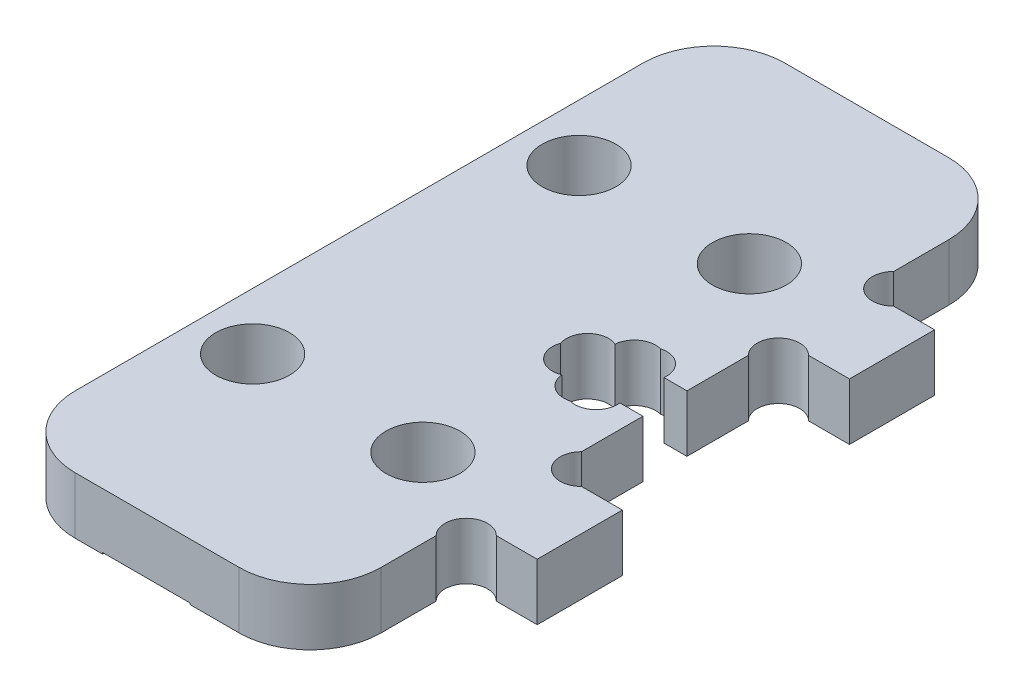
SolidWorks part; units mm, degrees
ref_plane "Alzado" through (0, 0, 0) normal (0, 0, 1) x (1, 0, 0)
ref_plane "Planta" through (0, 0, 0) normal (0, 1, 0) x (1, 0, 0)
ref_plane "Vista lateral" through (0, 0, 0) normal (1, 0, 0) x (0, 0, -1)
sketch "Croquis1" plane through (0, 0, 0) normal (0, 1, 0) x (1, 0, 0)
  line L0 (13.275, 14) -> (13.275, -14) construction
  line L1 (-5.775, -25) -> (5.775, -25)
  line L2 (-10.775, -20) -> (-10.775, 20)
  line L3 (-5.775, 25) -> (5.775, 25)
  line L4 (10.775, -20) -> (10.775, -14)
  line L5 (-10.775, -25) -> (10.775, 25) construction
  line L6 (-10.775, 25) -> (10.775, -25) construction
  line L7 (10.775, 14) -> (15.775, 14)
  line L8 (10.775, -8) -> (10.775, -1.55)
  line L9 (10.775, 8) -> (15.775, 8)
  line L10 (15.775, 14) -> (15.775, 8)
  line L11 (10.775, -8) -> (15.775, -8)
  line L12 (15.775, 11) -> (8.3263, 11) construction
  line L13 (10.775, -14) -> (15.775, -14)
  line L14 (15.775, -8) -> (15.775, -14)
  line L15 (0, 0) -> (13.275, 0) construction
  line L16 (10.775, 14) -> (10.775, 20)
  line L17 (8.725, -1.55) -> (8.725, -2.8)
  line L18 (5.825, 2.8) -> (8.725, 2.8)
  line L19 (5.825, 2.8) -> (5.825, 1.55)
  line L20 (5.825, -2.8) -> (8.725, -2.8)
  line L21 (8.725, 2.8) -> (8.725, 1.55)
  line L22 (3.775, 1.55) -> (5.825, 1.55)
  line L23 (3.775, 1.55) -> (3.775, -1.55)
  line L24 (3.775, -1.55) -> (5.825, -1.55)
  line L25 (10.775, 1.55) -> (10.775, 8)
  line L26 (8.725, 1.55) -> (10.775, 1.55)
  line L27 (5.825, -1.55) -> (5.825, -2.8)
  line L28 (8.725, -1.55) -> (10.775, -1.55)
  line L29 (3.775, 0) -> (0, 0) construction
  line L30 (7.275, 2.8) -> (7.275, -2.8) construction
  line L31 (7.275, 0) -> (3.775, 0) construction
  arc A0 (-5.775, -25) -> (-10.775, -20) centre (-5.775, -20) cw
  arc A1 (5.775, -25) -> (10.775, -20) centre (5.775, -20) ccw
  arc A2 (5.775, 25) -> (10.775, 20) centre (5.775, 20) cw
  arc A3 (-10.775, 20) -> (-5.775, 25) centre (-5.775, 20) cw
  point P0 (0, 0)
  dimension "D3" = 5
  dimension "D4" = 6
  dimension "D1" = 50
  dimension "D2" = 21.55
  dimension "D5" = 5
  dimension "D6" = 14
  dimension "D7" = 3.1
  dimension "D8" = 5.6
  dimension "D9" = 2.9
  dimension "D10" = 7
  dimension "D11" = 3.5
extrude "Saliente-Extruir1" add sketch "Croquis1" along normal blind 4
sketch "Croquis4" plane through (0, 0, 0) normal (0, 1, 0) x (1, 0, 0)
  line L1 (-3.85, 26.5) -> (2.3, 26.5)
  line L2 (-3.85, 26.5) -> (-3.85, -26.5)
  line L3 (-3.85, -26.5) -> (2.3, -26.5)
  line L4 (2.3, 26.5) -> (2.3, -26.5)
  line L6 (-0.775, 26.5) -> (-0.775, -26.5) construction
  line L7 (10.775, -20) -> (10.775, -14) construction
  line L8 (5.775, 25) -> (-5.775, 25) construction
  line L9 (-5.775, -25) -> (5.775, -25) construction
  dimension "D1" = 6.15
  dimension "D2" = 11.55
  dimension "D3" = 1.5
  dimension "D4" = 1.5
sketch "Croquis5" plane through (0, 4, 0) normal (0, 1, 0) x (1, 0, 0)
  line L0 (10.775, 0) -> (-10.775, 0) construction
  line L2 (-10.775, 20) -> (-10.775, -20) construction
  line L3 (-6.775, 11.5) -> (5.225, 11.5) construction
  line L4 (-0.775, 11.5) -> (-0.775, 26.5) construction
  line L6 (10.775, 8) -> (10.775, -8) construction
  circle A0 centre (-6.775, 11.5) radius 2.6
  circle A1 centre (5.225, 11.5) radius 2.6
  circle A2 centre (5.225, -11.5) radius 2.6
  circle A3 centre (-6.775, -11.5) radius 2.6
  dimension "D1" = 5.2
  dimension "D2" = 12
  dimension "D3" = 15
extrude "Cortar-Extruir3" cut sketch "Croquis5" against normal through all
sketch "Croquis9" plane through (0, 4, 0) normal (0, 1, 0) x (1, 0, 0)
  line L24 (-5.775, -25) -> (5.775, -25)
  line L25 (10.775, -20) -> (10.775, -14)
  line L26 (10.775, -14) -> (15.775, -14)
  line L27 (15.775, -14) -> (15.775, -8)
  line L28 (15.775, -8) -> (10.775, -8)
  line L29 (10.775, -8) -> (10.775, -1.55)
  line L30 (10.775, -1.55) -> (8.725, -1.55)
  line L31 (8.725, -1.55) -> (8.725, -2.8)
  line L32 (8.725, -2.8) -> (5.825, -2.8)
  line L33 (5.825, -2.8) -> (5.825, -1.55)
  line L34 (5.825, -1.55) -> (3.775, -1.55)
  line L35 (3.775, -1.55) -> (3.775, 1.55)
  line L36 (3.775, 1.55) -> (5.825, 1.55)
  line L37 (5.825, 1.55) -> (5.825, 2.8)
  line L38 (5.825, 2.8) -> (8.725, 2.8)
  line L39 (8.725, 2.8) -> (8.725, 1.55)
  line L40 (8.725, 1.55) -> (10.775, 1.55)
  line L41 (10.775, 1.55) -> (10.775, 8)
  line L42 (10.775, 8) -> (15.775, 8)
  line L43 (15.775, 8) -> (15.775, 14)
  line L44 (15.775, 14) -> (10.775, 14)
  line L45 (10.775, 14) -> (10.775, 20)
  line L46 (5.775, 25) -> (-5.775, 25)
  line L47 (-10.775, 20) -> (-10.775, -20)
  line L48 (-5.775, -25) -> (5.775, -25)
  line L49 (10.775, -20) -> (10.775, -14)
  line L50 (10.775, -14) -> (15.775, -14)
  line L51 (15.775, -14) -> (15.775, -8)
  line L52 (15.775, -8) -> (10.775, -8)
  line L53 (10.775, -8) -> (10.775, -1.55)
  line L54 (10.775, -1.55) -> (8.725, -1.55)
  line L55 (8.725, -1.55) -> (8.725, -2.8)
  line L56 (8.725, -2.8) -> (5.825, -2.8)
  line L57 (5.825, -2.8) -> (5.825, -1.55)
  line L58 (5.825, -1.55) -> (3.775, -1.55)
  line L59 (3.775, -1.55) -> (3.775, 1.55)
  line L60 (3.775, 1.55) -> (5.825, 1.55)
  line L61 (5.825, 1.55) -> (5.825, 2.8)
  line L62 (5.825, 2.8) -> (8.725, 2.8)
  line L63 (8.725, 2.8) -> (8.725, 1.55)
  line L64 (8.725, 1.55) -> (10.775, 1.55)
  line L65 (10.775, 1.55) -> (10.775, 8)
  line L66 (10.775, 8) -> (15.775, 8)
  line L67 (15.775, 8) -> (15.775, 14)
  line L68 (15.775, 14) -> (10.775, 14)
  line L69 (10.775, 14) -> (10.775, 20)
  line L70 (5.775, 25) -> (-5.775, 25)
  line L71 (-10.775, 20) -> (-10.775, -20)
  arc A4 (-10.775, -20) -> (-5.775, -25) centre (-5.775, -20) ccw
  arc A5 (5.775, -25) -> (10.775, -20) centre (5.775, -20) ccw
  arc A6 (10.775, 20) -> (5.775, 25) centre (5.775, 20) ccw
  arc A7 (-5.775, 25) -> (-10.775, 20) centre (-5.775, 20) ccw
  arc A8 (-10.775, -20) -> (-5.775, -25) centre (-5.775, -20) ccw
  arc A9 (5.775, -25) -> (10.775, -20) centre (5.775, -20) ccw
  arc A10 (10.775, 20) -> (5.775, 25) centre (5.775, 20) ccw
  arc A11 (-5.775, 25) -> (-10.775, 20) centre (-5.775, 20) ccw
  dimension "D1" = 0
sketch "Croquis6" plane through (0, 4, 0) normal (0, 1, 0) x (1, 0, 0)
  line L0 (3.775, 1.55) -> (5.825, 1.55) construction
  line L1 (3.775, -1.55) -> (3.775, 1.55) construction
  line L2 (5.825, -1.55) -> (3.775, -1.55) construction
  line L3 (3.775, 1.55) -> (5.275, 0.05)
  line L4 (3.775, -1.55) -> (5.275, -0.05)
  line L5 (5.825, 2.8) -> (8.725, 2.8) construction
  line L6 (5.825, 1.55) -> (5.825, 2.8) construction
  line L7 (5.825, 2.8) -> (7.325, 1.3)
  line L8 (8.725, 2.8) -> (8.725, 1.55) construction
  line L9 (8.725, 2.8) -> (7.225, 1.3)
  line L10 (5.825, -2.8) -> (5.825, -1.55) construction
  line L11 (8.725, -2.8) -> (5.825, -2.8) construction
  line L12 (5.825, -2.8) -> (7.325, -1.3)
  line L13 (8.725, -1.55) -> (8.725, -2.8) construction
  line L14 (8.725, -2.8) -> (7.225, -1.3)
  circle A0 centre (5.275, 0.05) radius 1.5
  circle A1 centre (5.275, -0.05) radius 1.5
  circle A2 centre (7.325, -1.3) radius 1.5
  circle A3 centre (7.225, -1.3) radius 1.5
  circle A4 centre (7.225, 1.3) radius 1.5
  circle A5 centre (7.325, 1.3) radius 1.5
  dimension "D1" = 3
sketch "Croquis7" plane through (0, 4, 0) normal (0, 1, 0) x (1, 0, 0)
  line L0 (3.775, 1.55) -> (5.275, 0.05) construction
  line L1 (3.775, -1.55) -> (5.275, -0.05) construction
  line L2 (5.825, -2.8) -> (7.325, -1.3) construction
  line L3 (8.725, -2.8) -> (7.225, -1.3) construction
  line L4 (8.725, 2.8) -> (7.225, 1.3) construction
  line L5 (5.825, 2.8) -> (7.325, 1.3) construction
  line L11 (9.1523, 1.55) -> (10.775, 1.55)
  line L12 (10.775, 1.55) -> (10.775, -1.55)
  line L13 (10.775, -1.55) -> (9.1523, -1.55)
  arc A0 (5.3925, 1.8822) -> (3.4177, 0) centre (4.8357, 0.4893) ccw
  arc A1 (3.4177, 0) -> (5.3925, -1.8822) centre (4.8357, -0.4893) ccw
  arc A2 (5.3925, -1.8822) -> (7.275, -3.1879) centre (6.8857, -1.7393) ccw
  arc A3 (7.275, -3.1879) -> (9.1523, -1.55) centre (7.6643, -1.7393) ccw
  arc A4 (9.1523, 1.55) -> (7.275, 3.1879) centre (7.6643, 1.7393) ccw
  arc A5 (7.275, 3.1879) -> (5.3925, 1.8822) centre (6.8857, 1.7393) ccw
  dimension "D1" = 3
extrude "Cortar-Extruir4" cut sketch "Croquis7" against normal through all
sketch "Croquis10" plane through (0, 4, 0) normal (0, 1, 0) x (1, 0, 0)
  line L0 (0, 0) -> (23.8324, 0) construction
  line L1 (15.775, 14) -> (10.775, 14) construction
  line L2 (10.775, 14) -> (10.775, 20) construction
  line L3 (10.775, 8) -> (15.775, 8) construction
  line L4 (10.775, 1.55) -> (10.775, 8) construction
  line L5 (10.775, 14) -> (12.275, 15.5) construction
  line L7 (10.775, 8) -> (12.275, 6.5) construction
  circle A0 centre (12.275, 15.5) radius 1.5 construction
  circle A1 centre (12.275, 6.5) radius 1.5 construction
  circle A2 centre (11.8357, 15.0607) radius 1.5
  circle A3 centre (11.8357, 6.9393) radius 1.5
  circle A4 centre (11.8357, -15.0607) radius 1.5
  circle A5 centre (11.8357, -6.9393) radius 1.5
  dimension "D1" = 3
extrude "Cortar-Extruir5" cut sketch "Croquis10" against normal through all
extrude "Cortar-Extruir6" cut sketch "Croquis4" along normal blind 0.1
